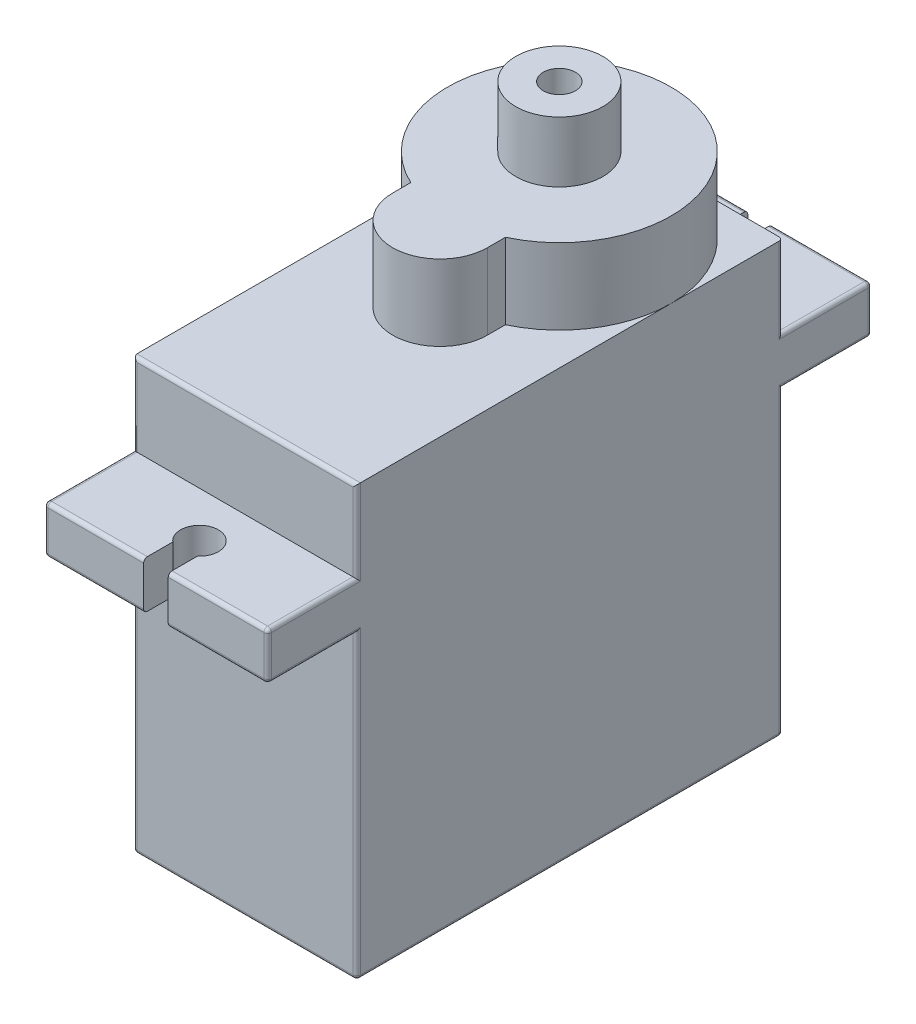
SolidWorks part; units mm, degrees
ref_plane "Plan de face" through (0, 0, 0) normal (0, 0, 1) x (1, 0, 0)
ref_plane "Plan de dessus" through (0, 0, 0) normal (0, 1, 0) x (1, 0, 0)
ref_plane "Plan de droite" through (0, 0, 0) normal (1, 0, 0) x (0, 0, -1)
sketch "Esquisse1" plane through (0, 0, 0) normal (0, 1, 0) x (1, 0, 0)
  line L1 (-5.9, -11.25) -> (5.9, -11.25)
  line L2 (-5.9, -11.25) -> (-5.9, 11.25)
  line L3 (-5.9, 11.25) -> (5.9, 11.25)
  line L4 (5.9, -11.25) -> (5.9, 11.25)
  line L5 (-5.9, -11.25) -> (5.9, 11.25) construction
  line L6 (-5.9, 11.25) -> (5.9, -11.25) construction
  point P0 (0, 0)
  dimension "D1" = 11.8
  dimension "D2" = 22.5
extrude "Boss.-Extru.1" add sketch "Esquisse1" along normal blind 15.9
sketch "Esquisse3" plane through (0, 15.9, 0) normal (0, 1, 0) x (1, 0, 0)
  line L0 (-5.9, 15.95) -> (-5.9, -15.95)
  line L1 (-5.9, 11.25) -> (-5.9, -11.25) construction
  line L2 (-5.9, -15.95) -> (-0.65, -15.95)
  line L3 (-0.65, -15.95) -> (-0.65, -14.4099)
  line L4 (-5.9, -11.25) -> (5.9, -11.25) construction
  line L5 (0.65, -14.4099) -> (0.65, -15.95)
  line L6 (0.65, -15.95) -> (5.9, -15.95)
  line L7 (5.9, -15.95) -> (5.9, 15.95)
  line L8 (5.9, -11.25) -> (5.9, 11.25) construction
  line L9 (-5.9, 0) -> (5.9, 0) construction
  line L10 (0.65, 15.95) -> (5.9, 15.95)
  line L11 (0.65, 14.4099) -> (0.65, 15.95)
  line L12 (-0.65, 15.95) -> (-0.65, 14.4099)
  line L13 (-5.9, 15.95) -> (-0.65, 15.95)
  arc A0 (-0.65, -14.4099) -> (0.65, -14.4099) centre (0, -13.65) cw
  arc A1 (-0.65, 14.4099) -> (0.65, 14.4099) centre (0, 13.65) ccw
  dimension "D4" = 1
  dimension "D1" = 4.7
  dimension "D2" = 2.3
  dimension "D3" = 1.3
extrude "Boss.-Extru.2" add sketch "Esquisse3" along normal blind 2.5
sketch "Esquisse4" plane through (0, 18.4, 0) normal (0, 1, 0) x (1, 0, 0)
  line L4 (5.9, -11.25) -> (5.9, 11.25)
  line L5 (-5.9, -11.25) -> (5.9, -11.25)
  line L6 (-5.9, 11.25) -> (-5.9, -11.25)
  line L7 (5.9, 11.25) -> (-5.9, 11.25)
  line L8 (5.9, -11.25) -> (5.9, 11.25)
  line L9 (-5.9, -11.25) -> (5.9, -11.25)
  line L10 (-5.9, 11.25) -> (-5.9, -11.25)
  line L11 (5.9, 11.25) -> (-5.9, 11.25)
  dimension "D1" = 0
extrude "Boss.-Extru.3" add sketch "Esquisse4" along normal blind 4.3
sketch "Esquisse5" plane through (0, 22.7, 0) normal (0, 1, 0) x (1, 0, 0)
  line L0 (0, 11.25) -> (0, -11.25) construction
  line L1 (5.9, 11.25) -> (-5.9, 11.25) construction
  line L2 (-5.9, -11.25) -> (5.9, -11.25) construction
  line L3 (2.5, -0.95) -> (-2.5, -0.95) construction
  line L4 (2.5, -0.95) -> (2.5, 0.0058)
  line L5 (-2.5, -0.95) -> (-2.5, 0.0058)
  line L6 (5.9, -3.45) -> (-5.9, -3.45) construction
  line L7 (5.9, -11.25) -> (5.9, 11.25) construction
  line L8 (-5.9, 11.25) -> (-5.9, -11.25) construction
  line L9 (-5.9, -11.25) -> (5.9, -11.25) construction
  arc A0 (2.5, 0.0058) -> (-2.5, 0.0058) centre (0, 5.35) ccw
  arc A1 (2.5, -0.95) -> (-2.5, -0.95) centre (0, -0.95) cw
  dimension "D1" = 5.9
  dimension "D2" = 2.5
  dimension "D3" = 7.8
extrude "Boss.-Extru.4" add sketch "Esquisse5" along normal blind 4
sketch "Esquisse6" plane through (0, 26.7, 0) normal (0, 1, 0) x (1, 0, 0)
  circle A0 centre (0, 5.35) radius 2.3
  arc A1 (2.5, 0.0058) -> (-2.5, 0.0058) centre (0, 5.35) ccw construction
  circle A2 centre (0, 5.35) radius 0.85
  dimension "D1" = 4.6
  dimension "D2" = 1.7
extrude "Boss.-Extru.5" add sketch "Esquisse6" along normal blind 3.2
fillet "Congé1" radius 0.2 33 edges at (0, 0, -11.25) (-5.9, 17.15, -15.95) (5.9, 17.15, -15.95) (3.275, 18.4, -15.95) (3.275, 15.9, -15.95) (-3.275, 18.4, -15.95) (-3.275, 15.9, -15.95) (0, 22.7, 11.25) (5.9, 17.15, 15.95) (3.275, 18.4, 15.95) (3.275, 15.9, 15.95) (-5.9, 17.15, 15.95) (-3.275, 18.4, 15.95) (-3.275, 15.9, 15.95) (5.9, 0, 0) (0, 0, 11.25) (-5.9, 0, 0)
